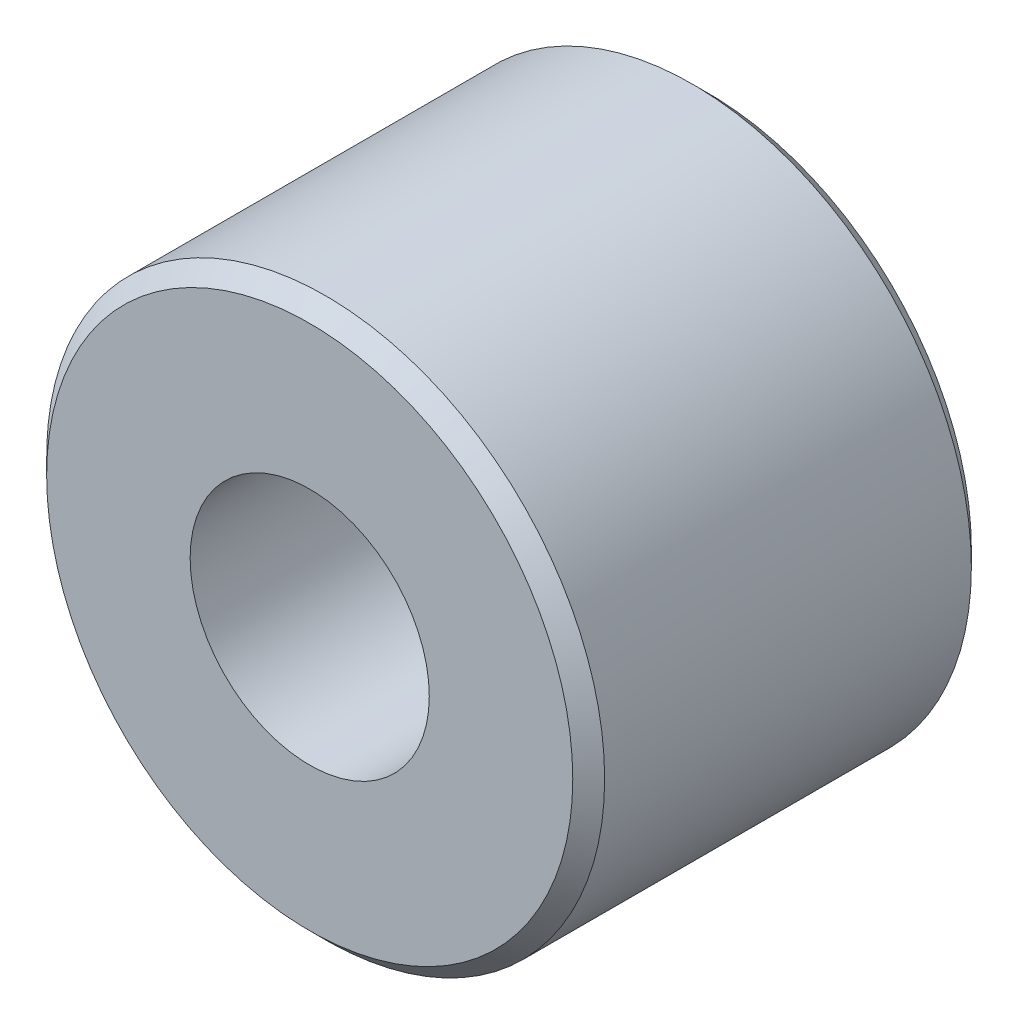
SolidWorks part; units mm, degrees
ref_plane "Plan1" through (0, 0, 0) normal (0, 0, 1) x (1, 0, 0)
ref_plane "Plan2" through (0, 0, 0) normal (0, 1, 0) x (1, 0, 0)
ref_plane "Plan3" through (0, 0, 0) normal (1, 0, 0) x (0, 0, -1)
sketch "Esquisse1" plane through (0, 0, 0) normal (0, 0, 1) x (1, 0, 0)
  circle A0 centre (0, 0) radius 1.5
  circle A1 centre (0, 0) radius 3.5
  dimension "D1" = 3
  dimension "D2" = 7
extrude "Base-Extrusion" add sketch "Esquisse1" along normal blind 5
chamfer "Chanfrein1" distance 0.2 angle 45
